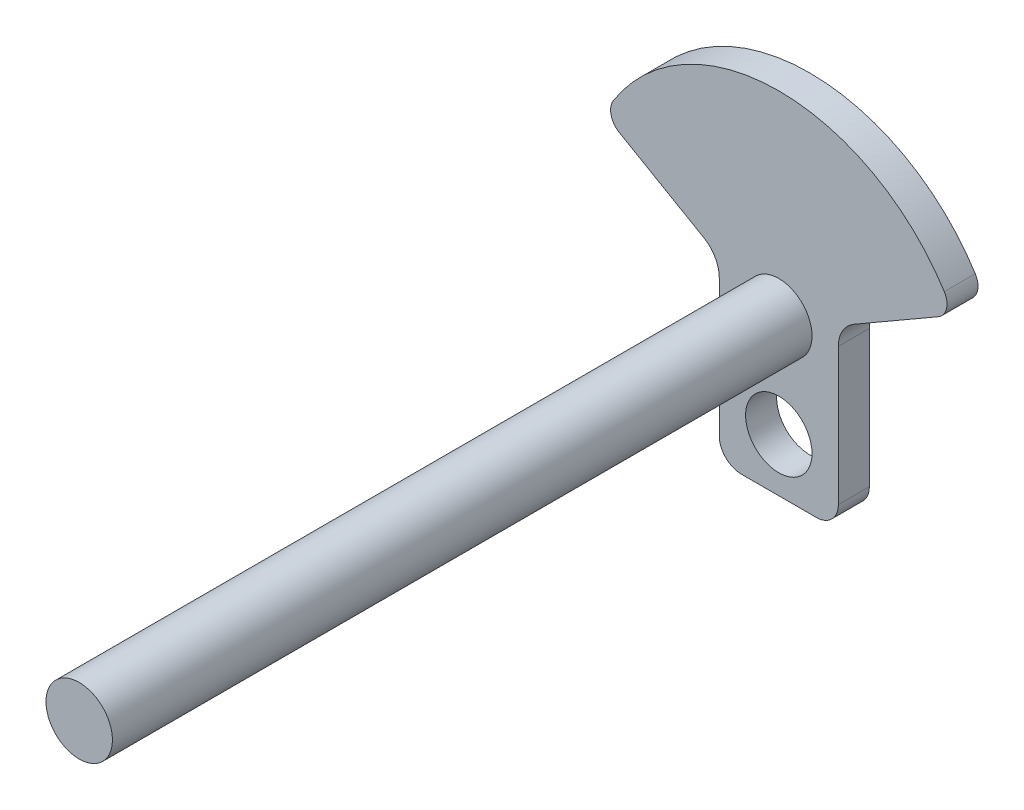
SolidWorks part; units mm, degrees
material "AISI 1020"
ref_plane "Front Plane" through (0, 0, 0) normal (0, 0, 1) x (1, 0, 0)
ref_plane "Top Plane" through (0, 0, 0) normal (0, 1, 0) x (1, 0, 0)
ref_plane "Right Plane" through (0, 0, 0) normal (1, 0, 0) x (0, 0, -1)
sketch "Sketch2" plane through (0, 0, 0) normal (0, 0, 1) x (1, 0, 0)
  line L0 (5, 0) -> (21.8951, 0)
  line L1 (26.8951, 5) -> (26.8951, 35.9585)
  line L2 (30.3951, 42.0207) -> (49.4401, 53.0164)
  line L3 (0, 5) -> (0, 35.9585)
  line L4 (-3.5, 42.0207) -> (-22.545, 53.0164)
  circle A1 centre (13.4476, 35) radius 7.5
  arc A2 (-23.9265, 58.6173) -> (50.8216, 58.6173) centre (13.4476, 35) cw
  arc A3 (21.8951, 0) -> (26.8951, 5) centre (21.8951, 5) ccw
  arc A4 (5, 0) -> (0, 5) centre (5, 5) cw
  arc A5 (30.3951, 42.0207) -> (26.8951, 35.9585) centre (33.8951, 35.9585) ccw
  arc A6 (0, 35.9585) -> (-3.5, 42.0207) centre (-7, 35.9585) ccw
  arc A7 (-23.9265, 58.6173) -> (-22.545, 53.0164) centre (-20.545, 56.4805) ccw
  arc A8 (50.8216, 58.6173) -> (49.4401, 53.0164) centre (47.4401, 56.4805) cw
  circle A9 centre (13.4476, 12) radius 7.5
  point P13 (26.8951, 0)
  point P16 (0, 0)
  point P19 (26.8951, 40)
  point P22 (0, 40)
  point P25 (-25.9808, 55)
  point P28 (52.8759, 55)
  dimension "D2" = 30
  dimension "D3" = 12
  dimension "D8" = 44.2108
  dimension "D9" = 5
  dimension "D10" = 7
  dimension "D11" = 4
  dimension "D1" = 30
  dimension "D4" = 120
  dimension "D5" = 40
  dimension "D6" = 40
  dimension "D7" = 35
extrude "Boss-Extrude5" add sketch "Sketch2" along normal blind 7 contours L2 A8 A2 A7 L4 A6 L3 A4 L0 A3 L1 A5 | A1 | A9
sketch "Sketch5" plane through (0, 0, 0) normal (0, 0, -1) x (-1, 0, 0)
  circle A0 centre (-13.4476, 35) radius 7.5
extrude "Boss-Extrude6" add sketch "Sketch5" against normal blind 165
